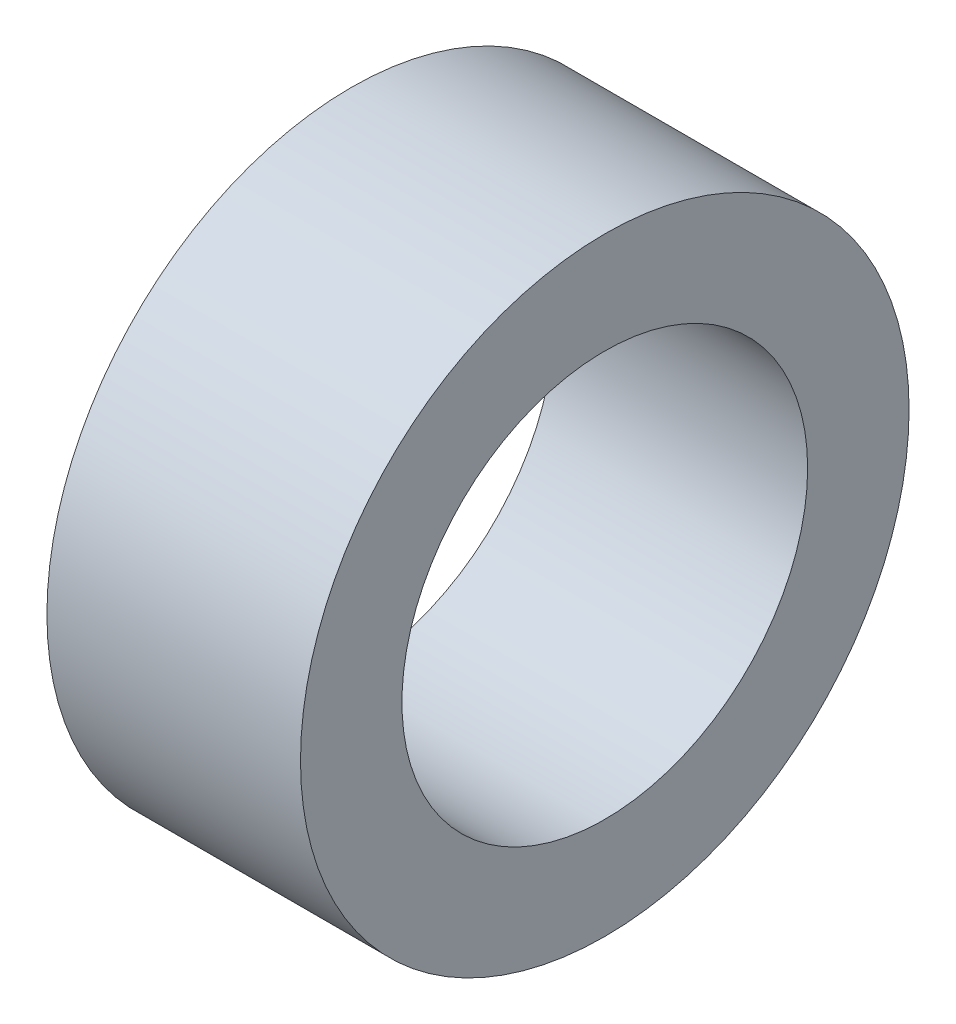
SolidWorks part; units mm, degrees
material "Brass"
ref_plane "Front Plane" through (0, 0, 0) normal (0, 0, 1) x (1, 0, 0)
ref_plane "Top Plane" through (0, 0, 0) normal (0, 1, 0) x (1, 0, 0)
ref_plane "Right Plane" through (0, 0, 0) normal (1, 0, 0) x (0, 0, -1)
sketch "Sketch1" plane through (0, 0, 0) normal (1, 0, 0) x (0, 0, -1)
  circle A0 centre (0, 0) radius 5.08
  circle A1 centre (0, 0) radius 7.62
  dimension "D1" = 10.16
  dimension "D2" = 15.24
extrude "Boss-Extrude1" add sketch "Sketch1" along normal blind 6.35
